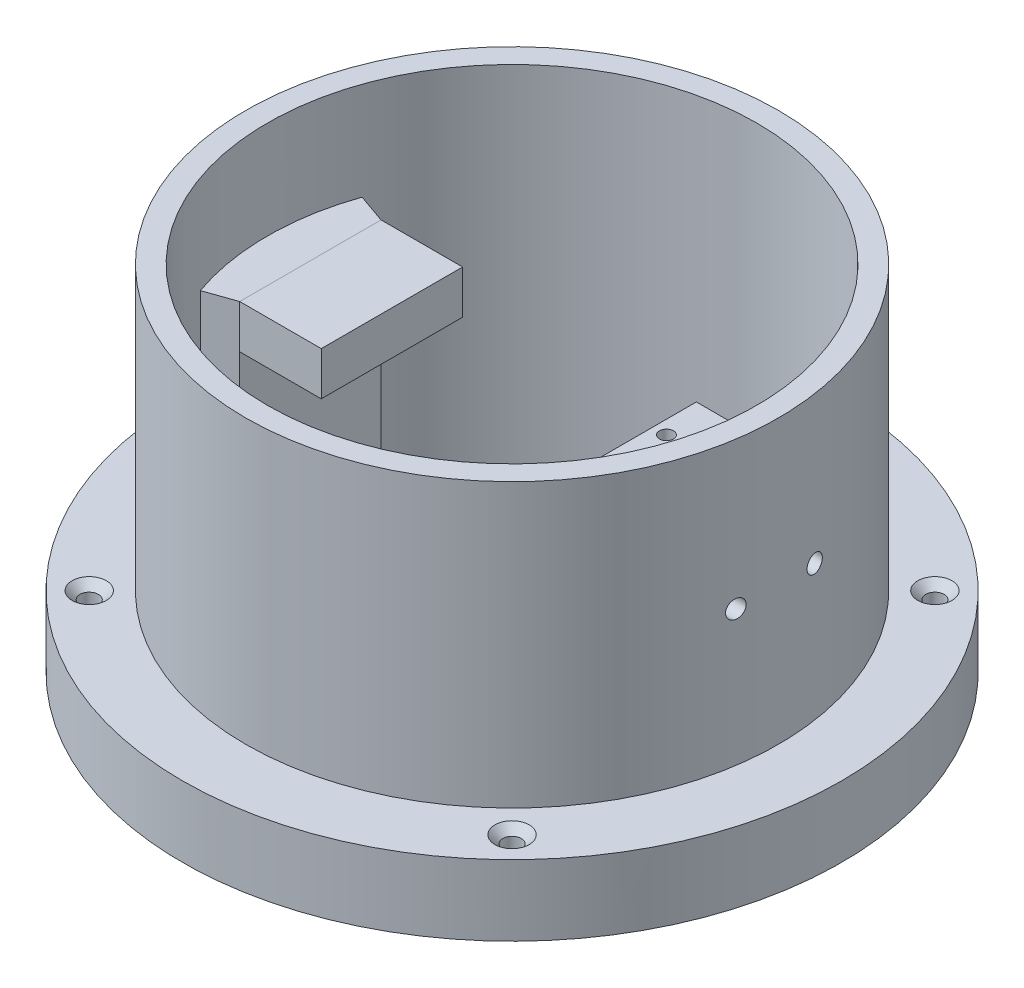
SolidWorks part; units mm, degrees
ref_plane "Front Plane" through (0, 0, 0) normal (0, 0, 1) x (1, 0, 0)
ref_plane "Top Plane" through (0, 0, 0) normal (0, 1, 0) x (1, 0, 0)
ref_plane "Right Plane" through (0, 0, 0) normal (1, 0, 0) x (0, 0, -1)
sketch "Sketch1" plane through (0, 0, 0) normal (0, 1, 0) x (1, 0, 0)
  circle A0 centre (0, 0) radius 60.625
  circle A1 centre (0, 0) radius 45
  dimension "D1" = 121.25
  dimension "D2" = 90
extrude "Boss-Extrude1" add sketch "Sketch1" along normal blind 4 contours A0
sketch "Sketch2" plane through (0, 4, 0) normal (0, 1, 0) x (1, 0, 0)
  circle A0 centre (0, 0) radius 45 construction
  circle A1 centre (0, 0) radius 45
  circle A2 centre (0, 0) radius 49
  dimension "D1" = 4
extrude "Boss-Extrude2" add sketch "Sketch2" along normal blind 52
ref_plane "Plane1" through (0, 36, 0) normal (0, 1, 0) x (1, 0, 0)
sketch "Sketch4" plane through (0, 0, 0) normal (0, 0, 1) x (1, 0, 0)
  line L0 (-60.625, 0) -> (60.625, 0) construction
  line L1 (20.9, 38) -> (28.9, 38)
  line L2 (20.9, 38) -> (20.9, 0)
  line L3 (20.9, 0) -> (28.9, 0)
  line L4 (28.9, 38) -> (28.9, 0)
  line L5 (49, 56) -> (-49, 56) construction
  line L6 (-45, 0) -> (-45, 4)
  line L7 (-22.1, 38) -> (-37.1, 38)
  line L8 (-22.1, 38) -> (-22.1, 30)
  line L9 (-22.1, 30) -> (-37.1, 30)
  line L10 (-37.1, 38) -> (-37.1, 30)
  line L11 (60.625, 4) -> (-60.625, 4) construction
  line L12 (-22.1, 30) -> (-45, 7.1)
  dimension "D1" = 20.9
  dimension "D2" = 8
  dimension "D3" = 18
  dimension "D4" = 43
  dimension "D5" = 15
  dimension "D6" = 8
  dimension "D7" = 45
  dimension "D8" = 18
extrude "Boss-Extrude4" add sketch "Sketch4" along normal mid plane 26 contours L9 L8 L7 L6 | L12 L9 L6 | L1 L4 L3 L2
sketch "Sketch5" plane through (0, 0, 0) normal (0, -1, 0) x (1, 0, 0)
  line L0 (20.9, 13) -> (29.0674, 34.3524)
  line L1 (20.9, -13) -> (29.0674, -34.3524)
  line L2 (20.9, 13) -> (20.9, -13)
  circle A0 centre (0, 0) radius 45 construction
  arc A1 (29.0674, -34.3524) -> (29.0674, 34.3524) centre (0, 0) ccw
extrude "Boss-Extrude5" add sketch "Sketch5" against normal up to surface (4 mm away) contours L0 A1 L1 L2 up to face at (0, 4, 60.625)
sketch "Sketch7" plane through (0, 38, 0) normal (0, 1, 0) x (1, 0, 0)
  line L0 (-22.1, -13) -> (-22.1, 13) construction
  circle A0 centre (-24.6, 5) radius 1.3
  circle A1 centre (-24.6, -5) radius 1.3
  circle A2 centre (23.4, 5) radius 1.3
  circle A3 centre (23.4, -5) radius 1.3
  dimension "D1" = 2.6
  dimension "D2" = 2.6
  dimension "D3" = 10
  dimension "D4" = 5
  dimension "D5" = 2.5
  dimension "D7" = 48
  dimension "D6" = 2
extrude "Cut-Extrude4" cut sketch "Sketch7" against normal blind 7.2
sketch "Sketch9" plane through (20.9, 0, 0) normal (-1, 0, 0) x (0, 0, 1)
  line L0 (13, 0) -> (-13, 0) construction
  line L1 (-5, 29) -> (5, 29)
  line L2 (-5, 29) -> (-5, 0)
  line L3 (-5, 0) -> (5, 0)
  line L4 (5, 29) -> (5, 0)
  line L5 (-5, 29) -> (5, 0) construction
  line L6 (-5, 0) -> (5, 29) construction
  line L7 (0, 0) -> (0, 29) construction
  line L8 (13, 38) -> (-13, 38) construction
  line L10 (5, 5) -> (-5, 5)
  point P0 (0, 14.5)
  dimension "D1" = 10
  dimension "D2" = 9
  dimension "D3" = 5
extrude "Cut-Extrude7" cut sketch "Sketch9" against normal up to surface (8 mm away) contours L10 L4 L1 L2 up to face at (28.9, 21, 0)
sketch "Sketch12" plane through (0, 4, 0) normal (0, 1, 0) x (1, 0, 0)
  line L5 (36.9, 2.7185) -> (36.9, -2.7185)
  line L7 (36.9, 2.7185) -> (36.9, -2.7185)
  line L9 (33.9, 16.0926) -> (33.9, -16.0926)
  line L10 (28.9, -13) -> (28.9, 13) construction
  arc A2 (36.9, -2.7185) -> (36.9, 2.7185) centre (0, 0) ccw
  arc A3 (36.9, -2.7185) -> (36.9, 2.7185) centre (0, 0) ccw
  dimension "D2" = 5
  dimension "D1" = 8
extrude "Cut-Extrude9" cut sketch "Sketch12" against normal through all
sketch "Sketch14" plane through (0, 4, 0) normal (0, 1, 0) x (1, 0, 0)
  line L0 (0, 0) -> (-38.8909, 38.8909) construction
  circle A0 centre (-38.8909, 38.8909) radius 1.5
  circle A1 centre (38.8909, 38.8909) radius 1.5
  circle A2 centre (38.8909, -38.8909) radius 1.5
  circle A3 centre (-38.8909, -38.8909) radius 1.5
  point P15 (0, 0)
  dimension "D1" = 3
  dimension "D2" = 55
  dimension "D4" = 4
hole_wizard "CSK for M3 Countersunk Flat Head Screw1" positions "Sketch15" profile "Sketch17" countersink size "M3" standard "DIN" end condition up to next
sketch "Sketch15" plane through (0, 4, 0) normal (0, 1, 0) x (1, 0, 0)
  point P0 (-38.8909, 38.8909)
  point P3 (-38.8909, -38.8909)
  point P6 (38.8909, -38.8909)
  point P9 (38.8909, 38.8909)
sketch "Sketch17" plane through (-38.8909, 4, -38.8909) normal (1, 0, 0) x (0, 0, 1)
  line L0 (0, 0) -> (0, 4.001)
  line L1 (0, 4.001) -> (1.7, 4.001)
  line L2 (1.7, 4.001) -> (1.7, 1.45)
  line L3 (1.7, 1.45) -> (3.15, 0)
  line L5 (3.15, 0) -> (0, 0)
  line L6 (-1.7, 1.45) -> (-3.15, 0) construction
  line L11 (0, -6.35) -> (0, 107.95) construction
  dimension "Thru Hole Dia." = 3.4
  dimension "Thru Hole Depth" = 4.001
  dimension "Near C'Sink Dia." = 6.3
  dimension "Near C'Sink Angle" = 90
sketch "Croquis3" plane through (0, 0, 0) normal (0, -1, 0) x (1, 0, 0)
  line L0 (28.9, 13) -> (41.0295, 18.4819)
  line L1 (28.9, -13) -> (41.0391, -18.4605)
  line L2 (-37.1, 13) -> (-42.4683, 14.8811)
  line L3 (-37.1, -13) -> (-42.4683, -14.8811)
  line L4 (-37.1, 13) -> (-37.1, -13)
  line L5 (28.9, 13) -> (28.9, -13)
  line L6 (41.0295, 18.4819) -> (41.0391, -18.4605)
  circle A0 centre (0, 0) radius 45 construction
  arc A1 (-42.4683, -14.8811) -> (-42.4683, 14.8811) centre (0, 0) cw
extrude "Saliente-Extruir1" add sketch "Croquis3" against normal blind 38
sketch "Croquis6" plane through (0, 0, 0) normal (0, 1, 0) x (1, 0, 0)
  line L0 (41.0391, 18.4605) -> (43.8401, 18.4605)
  line L1 (43.8401, 18.4605) -> (46.5236, 6.2681)
  line L2 (46.5236, 6.2681) -> (46.5236, -4.6651)
  line L3 (46.5236, -4.6651) -> (45, -15.5151)
  line L4 (45, -15.5151) -> (44.5833, -18.4828)
  line L5 (44.5833, -18.4828) -> (41.0295, -18.4819)
  line L6 (41.0295, -18.4819) -> (41.0391, 18.4605)
extrude "Saliente-Extruir2" add sketch "Croquis6" along normal blind 38
sketch "Croquis7" plane through (0, 0, 0) normal (0, -1, 0) x (1, 0, 0)
  circle A0 centre (34.1155, 0) radius 7.5
  dimension "D1" = 15
extrude "Cortar-Extruir1" cut sketch "Croquis7" against normal blind 38
sketch "Croquis9" plane through (20.9, 0, 0) normal (-1, 0, 0) x (0, 0, 1)
  line L0 (13, 38) -> (13, 0) construction
  line L1 (13, 38) -> (-13, 38) construction
  circle A0 centre (-7.23, 28.95) radius 1.65
  circle A1 centre (7.27, 28.95) radius 1.65
  dimension "D1" = 3.3
  dimension "D2" = 3.3
  dimension "D3" = 5.73
  dimension "D4" = 9.05
  dimension "D5" = 9.05
  dimension "D6" = 14.5
extrude "Cortar-Extruir2" cut sketch "Croquis9" against normal through all
sketch "Croquis12" plane through (0, 0, 0) normal (0, -1, 0) x (1, 0, 0)
  circle A0 centre (0, 0) radius 60.625
  circle A1 centre (0, 0) radius 45
extrude "Saliente-Extruir4" add sketch "Croquis12" along normal blind 9
sketch "Croquis14" plane through (0, 4, 0) normal (0, 1, 0) x (1, 0, 0)
  circle A0 centre (-38.8909, 38.8909) radius 1.7
  circle A1 centre (38.8909, 38.8909) radius 1.7
  circle A2 centre (38.8909, -38.8909) radius 1.7
  circle A3 centre (-38.8909, -38.8909) radius 1.7
extrude "Cortar-Extruir4" cut sketch "Croquis14" against normal through all
